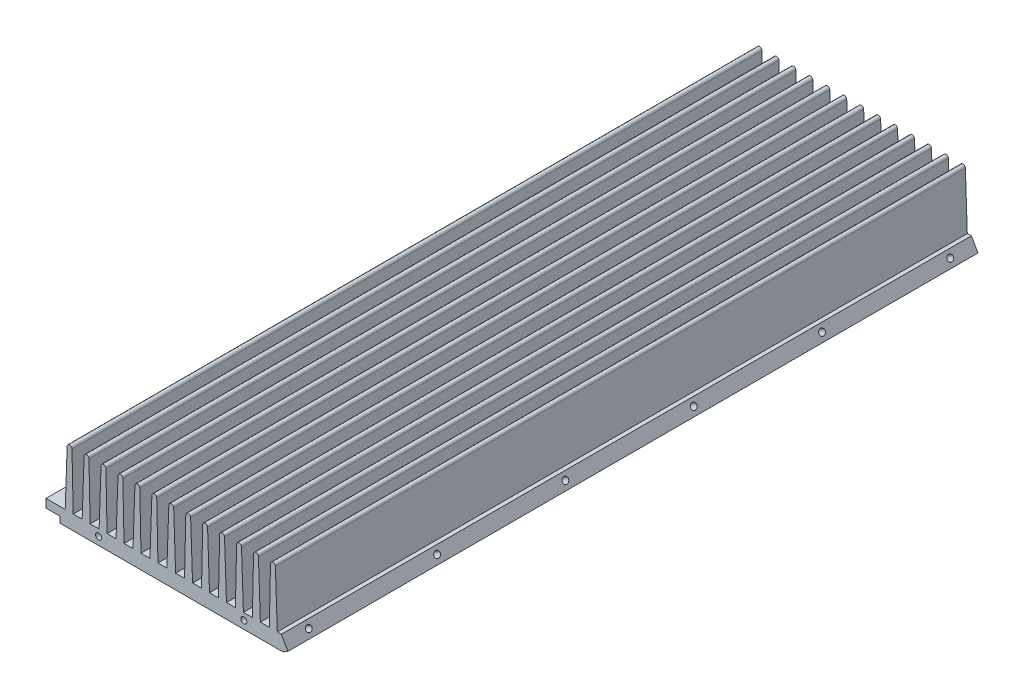
SolidWorks part; units mm, degrees
ref_plane "Plano frontal" through (0, 0, 0) normal (0, 0, 1) x (1, 0, 0)
ref_plane "Plano superior" through (0, 0, 0) normal (0, 1, 0) x (1, 0, 0)
ref_plane "Plano direito" through (0, 0, 0) normal (1, 0, 0) x (0, 0, -1)
sketch "Esboço1" plane through (0, 0, 0) normal (0, 0, 1) x (1, 0, 0)
  line L3 (0, 0) -> (-113, 0)
  line L102 (-76, 6) -> (-72.3, 6)
  line L103 (-83, 6) -> (-79.3, 6)
  line L104 (-86.3, 6) -> (-90, 6)
  line L115 (-56.5, 0) -> (-56.5, 30) construction
  line L116 (-113, 30) -> (15.3408, 30) construction
  line L146 (-86.3, 6) -> (-85.5, 29)
  line L147 (-83.5, 29) -> (-83, 6)
  line L148 (-85.5, 29) -> (-83.5, 29) construction
  line L149 (-90, 6) -> (-90.5, 29)
  line L150 (-92.5, 29) -> (-93.3, 6)
  line L151 (-48.5, 29) -> (-50.5, 29) construction
  line L152 (-93.3, 6) -> (-97, 6)
  line L153 (-97, 6) -> (-97.5, 29)
  line L154 (-99.5, 29) -> (-100.3, 6)
  line L155 (-79.3, 6) -> (-78.5, 29)
  line L156 (-76.5, 29) -> (-76, 6)
  line L161 (-78.5, 29) -> (-76.5, 29) construction
  line L162 (-72.3, 6) -> (-71.5, 29)
  line L163 (-100.3, 6) -> (-104, 6)
  line L164 (-71.5, 29) -> (-69.5, 29) construction
  line L165 (-69.5, 29) -> (-69, 6)
  line L167 (-104, 6) -> (-104.5, 29)
  line L169 (-8.5, 29) -> (-6.5, 29) construction
  line L170 (-90.5, 29) -> (-92.5, 29) construction
  line L171 (-97.5, 29) -> (-99.5, 29) construction
  line L172 (-104.5, 29) -> (-106.5, 29) construction
  line L173 (-15.5, 29) -> (-13.5, 29) construction
  line L174 (-22.5, 29) -> (-20.5, 29) construction
  line L175 (-107.3, 6) -> (-106.5, 29)
  line L176 (-113, 0) -> (-113, 30)
  line L177 (-113, 30) -> (-111, 30)
  line L178 (-111, 30) -> (-111, 6)
  line L179 (-111, 6) -> (-107.3, 6)
  line L181 (-57.5, 29) -> (-55.5, 29) construction
  line L183 (-69, 6) -> (-65.3, 6)
  line L184 (-65.3, 6) -> (-64.5, 29)
  line L185 (-64.5, 29) -> (-62.5, 29) construction
  line L186 (-62.5, 29) -> (-62, 6)
  line L187 (-62, 6) -> (-58.3, 6)
  line L188 (-58.3, 6) -> (-57.5, 29)
  line L189 (-41.5, 29) -> (-43.5, 29) construction
  line L190 (-34.5, 29) -> (-36.5, 29) construction
  line L191 (-27.5, 29) -> (-29.5, 29) construction
  line L192 (-54.7, 6) -> (-55.5, 29)
  line L193 (-51, 6) -> (-54.7, 6)
  line L194 (-50.5, 29) -> (-51, 6)
  line L195 (-47.7, 6) -> (-48.5, 29)
  line L196 (-44, 6) -> (-47.7, 6)
  line L197 (-2, 6) -> (-5.7, 6)
  line L198 (-2, 30) -> (-2, 6)
  line L199 (0, 30) -> (-2, 30)
  line L200 (0, 0) -> (0, 30)
  line L201 (-5.7, 6) -> (-6.5, 29)
  line L202 (-9, 6) -> (-8.5, 29)
  line L203 (-43.5, 29) -> (-44, 6)
  line L204 (-12.7, 6) -> (-9, 6)
  line L205 (-40.7, 6) -> (-41.5, 29)
  line L206 (-36.5, 29) -> (-37, 6)
  line L207 (-33.7, 6) -> (-34.5, 29)
  line L208 (-13.5, 29) -> (-12.7, 6)
  line L209 (-16, 6) -> (-15.5, 29)
  line L210 (-19.7, 6) -> (-16, 6)
  line L211 (-20.5, 29) -> (-19.7, 6)
  line L212 (-23, 6) -> (-22.5, 29)
  line L213 (-29.5, 29) -> (-30, 6)
  line L214 (-26.7, 6) -> (-27.5, 29)
  line L215 (-26.7, 6) -> (-23, 6)
  line L216 (-30, 6) -> (-33.7, 6)
  line L217 (-37, 6) -> (-40.7, 6)
  arc A4 (-85.5, 29) -> (-83.5, 29) centre (-84.5, 29) cw
  arc A6 (-78.5, 29) -> (-76.5, 29) centre (-77.5, 29) cw
  arc A8 (-71.5, 29) -> (-69.5, 29) centre (-70.5, 29) cw
  arc A20 (-90.5, 29) -> (-92.5, 29) centre (-91.5, 29) ccw
  arc A21 (-99.5, 29) -> (-97.5, 29) centre (-98.5, 29) cw
  arc A22 (-106.5, 29) -> (-104.5, 29) centre (-105.5, 29) cw
  arc A29 (-57.5, 29) -> (-55.5, 29) centre (-56.5, 29) cw
  arc A30 (-64.5, 29) -> (-62.5, 29) centre (-63.5, 29) cw
  arc A31 (-48.5, 29) -> (-50.5, 29) centre (-49.5, 29) ccw
  arc A32 (-6.5, 29) -> (-8.5, 29) centre (-7.5, 29) ccw
  arc A33 (-13.5, 29) -> (-15.5, 29) centre (-14.5, 29) ccw
  arc A34 (-22.5, 29) -> (-20.5, 29) centre (-21.5, 29) cw
  arc A35 (-41.5, 29) -> (-43.5, 29) centre (-42.5, 29) ccw
  arc A36 (-34.5, 29) -> (-36.5, 29) centre (-35.5, 29) ccw
  arc A37 (-27.5, 29) -> (-29.5, 29) centre (-28.5, 29) ccw
  point P43 (-56.5, 30)
  dimension "D2" = 1
  dimension "D1" = 7
  dimension "D3" = 3.7
  dimension "D4" = 2
  dimension "D5" = 6
  dimension "D6" = 113
  dimension "D8" = 30
extrude "Ressalto-extrusão1" add sketch "Esboço1" along normal blind 285
sketch "Esboço2" plane through (0, 0, 285) normal (0, 0, 1) x (1, 0, 0)
  line L5 (-102.5538, 0) -> (-10.4462, 0) construction
  line L6 (-102.8905, 6) -> (-108.2341, 6)
  line L16 (-108.2341, 6) -> (-108.2341, 2.5)
  line L22 (-108.2341, 2.5) -> (-102.5538, 2.5)
  line L23 (-8.2811, 1.25) -> (-10.4462, 0)
  line L25 (-102.5538, 2.5) -> (-102.5538, 0)
  line L26 (-100.3, 6) -> (-104, 6) construction
  line L27 (-113, 0) -> (0, 0) construction
  line L28 (-10.4462, 0) -> (0, 0)
  line L29 (0, 0) -> (0, 38.5588)
  line L30 (0, 38.5588) -> (-11.4168, 38.5588)
  line L31 (-11.4168, 38.5588) -> (-11.4168, 6.6812)
  line L34 (-11.4168, 6.6812) -> (-8.2811, 1.25)
  line L48 (-102.8905, 6) -> (-102.8905, 31.5406)
  line L49 (-102.8905, 31.5406) -> (-125.5568, 31.5406)
  line L50 (-125.5568, 31.5406) -> (-125.5568, -3.4367)
  line L51 (-125.5568, -3.4367) -> (-107.9645, -3.4367)
  line L52 (-107.9645, -3.4367) -> (-102.5538, 0)
  point P13 (-56.5, 0)
  point P14 (-56.5, 0)
  dimension "D1" = 92.1077
  dimension "D2" = 3.5
  dimension "D4" = 150
  dimension "D6" = 2.5
extrude "Corte-extrusão1" cut sketch "Esboço2" against normal through all both and the other way through all
sketch "Esboço11" [suppressed] plane through (0, 0, 285) normal (0, 0, 1) x (1, 0, 0)
  line L0 (-8.9831, 2.5341) -> (-8.2505, 1.2653)
  line L1 (-8.2505, 1.2653) -> (-10.4462, 0)
  line L2 (-10.4462, 0) -> (-11.3698, 0)
  line L4 (-11.3698, 0) -> (-10.7953, 3.3074)
  line L5 (-10.7953, 3.3074) -> (-8.9831, 2.5341)
  dimension "D1" = 8.2505
  dimension "D2" = 1.2653
  dimension "D3" = 2.1956
  dimension "D4" = 1.2653
  dimension "D5" = 1.2688
  dimension "D6" = 0.7326
extrude "Ressalto-extrusão5" [suppressed] add sketch "Esboço11" against normal blind 285
sketch "Esboço9" [suppressed] plane through (0, 0, 285) normal (0, 0, 1) x (1, 0, 0)
  line L2 (-6.9821, 6) -> (-8.9831, 2.5341) construction
  line L4 (-8.9821, 2.5359) -> (-10.9821, 6)
  line L5 (-16, 6) -> (-19.7, 6) construction
  line L6 (-10.9821, 6) -> (-6.9821, 6)
  line L7 (-6.9821, 6) -> (-8.9821, 2.5359)
  dimension "D1" = 4
sketch "Esboço3" [suppressed] plane through (0, 0, 285) normal (0, 0, 1) x (1, 0, 0)
  line L1 (-97, 6) -> (-122.3763, 6)
  line L2 (-97, 6) -> (-97, 40.0777)
  line L3 (-97, 40.0777) -> (-122.3763, 40.0777)
  line L4 (-122.3763, 6) -> (-122.3763, 40.0777)
  line L5 (-16, 6) -> (6.6432, 6)
  line L6 (-16, 6) -> (-16, 36.7002)
  line L7 (-16, 36.7002) -> (6.6432, 36.7002)
  line L8 (6.6432, 6) -> (6.6432, 36.7002)
extrude "Corte-extrusão2" [suppressed] cut sketch "Esboço3" against normal through all both and the other way through all
sketch "Esboço4" plane through (0, 0, 285) normal (0, 0, 1) x (1, 0, 0)
  line L0 (-56.5, 30) -> (-56.5, 0) construction
  line L1 (-102.5538, 0) -> (-10.4462, 0) construction
  line L2 (-86.5, 3.2348) -> (-56.5, 3.2348) construction
  line L3 (-56.5, 3.2348) -> (-26.5, 3.2348) construction
  circle A0 centre (-26.5, 3.2348) radius 1.25
  circle A1 centre (-86.5, 3.2348) radius 1.25
  arc A2 (-55.5, 29) -> (-57.5, 29) centre (-56.5, 29) ccw construction
  dimension "D3" = 2.5
  dimension "D1" = 30
  dimension "D2" = 3.2348
extrude "Corte-extrusão3" cut sketch "Esboço4" against normal blind 10
sketch "Esboço5" [suppressed] plane through (0, 6, 0) normal (0, 1, 0) x (1, 0, 0)
  line L0 (-99.0329, -274.5) -> (-99.0329, -208.5) construction
  line L1 (-99.0329, -208.5) -> (-99.0329, -142.5) construction
  line L2 (-99.0329, -142.5) -> (-99.0329, -76.5) construction
  line L3 (-99.0329, -76.5) -> (-99.0329, -10.5) construction
  line L4 (-106.0179, 0) -> (-106.0179, -285) construction
  line L5 (-100.3, -285) -> (-113, -285) construction
  circle A0 centre (-99.0329, -274.5) radius 1.25
  circle A1 centre (-99.0329, -208.5) radius 1.25
  circle A2 centre (-99.0329, -142.5) radius 1.25
  circle A3 centre (-99.0329, -76.5) radius 1.25
  circle A4 centre (-99.0329, -10.5) radius 1.25
  circle A5 centre (-12.4646, -20.5) radius 1.25
  circle A6 centre (-12.4646, -101.8333) radius 1.25
  circle A7 centre (-12.4646, -183.1667) radius 1.25
  circle A8 centre (-12.4646, -264.5) radius 1.25
  dimension "D1" = 2.5
  dimension "D3" = 10.5
  dimension "D2" = 6.985
  dimension "D4" = 66
extrude "Corte-extrusão4" [suppressed] cut sketch "Esboço5" against normal blind 5
sketch "Esboço6" [suppressed] plane through (0, 0, 0) normal (0, 0, -1) x (-1, 0, 0)
  line L0 (6.9821, 6) -> (10.4462, 0) construction
  line L1 (8.7141, 3) -> (104.2859, 3) construction
  line L2 (102.5538, 0) -> (106.0179, 6) construction
  line L3 (103.7085, 2) -> (9.2915, 2)
  line L4 (9.2915, 2) -> (8.1368, 4)
  line L5 (8.1368, 4) -> (104.8632, 4)
  line L6 (104.8632, 4) -> (103.7085, 2)
  line L7 (102.5538, 0) -> (106.0179, 6) construction
  line L8 (6.9821, 6) -> (10.4462, 0) construction
  line L9 (6.9821, 6) -> (19.7, 6) construction
  point P11 (104.2859, 3)
  dimension "D1" = 1
  dimension "D2" = 1
extrude "Ressalto-extrusão2" [suppressed] add sketch "Esboço6" along normal blind 1
sketch "Esboço7" plane through (0, 0, 0) normal (0, -1, 0) x (-1, 0, 0)
  line L0 (49.75, -279) -> (49.75, -275.2034) construction
  line L1 (49.75, -275.2034) -> (63.25, -275.2034) construction
  line L2 (102.5538, -285) -> (10.4462, -285) construction
  line L3 (63.25, -275.2034) -> (63.25, -279) construction
  line L6 (56.5, -275.2034) -> (56.5, -279) construction
  line L7 (10.4462, -279) -> (102.5538, -279) construction
  line L8 (10.4462, 0) -> (10.4462, -285) construction
  line L9 (102.5538, 0) -> (102.5538, -285) construction
  circle A0 centre (95, -28.5) radius 1.65
  circle A1 centre (71.949, -28.592) radius 1.25
  circle A2 centre (72.33, -10.685) radius 1.25
  circle A3 centre (30.928, -51.5) radius 1.25
  circle A4 centre (24, -15) radius 1.65
  circle A5 centre (34.738, -79.011) radius 1.25
  circle A6 centre (18.355, -144.416) radius 1.65
  circle A7 centre (20, -249) radius 1.65
  circle A8 centre (35.246, -237) radius 1.25
  circle A9 centre (93, -249) radius 1.65
  circle A10 centre (78.807, -182.77) radius 1.25
  circle A11 centre (82.363, -100.093) radius 1.25
  circle A12 centre (29.404, -176.293) radius 1.25
  circle A13 centre (39, -220) radius 1.25
  circle A14 centre (39, -200) radius 1.25
  circle A15 centre (39, -180) radius 1.25
  circle A16 centre (39, -160) radius 1.25
  circle A17 centre (74, -130) radius 1.25
  circle A18 centre (74, -110) radius 1.25
  circle A19 centre (74, -90) radius 1.25
  circle A20 centre (74, -70) radius 1.25
  circle A21 centre (92.7378, -168.3478) radius 1.25
  circle A22 centre (94.207, -195.6022) radius 1.25
  circle A23 centre (89.5041, -51.5) radius 1.25
  circle A28 centre (49.75, -279) radius 1.25
  circle A29 centre (63.25, -279) radius 1.25
  dimension "D1" = 3.3
  dimension "D2" = 2.5
  dimension "D3" = 2.5
  dimension "D4" = 2.5
  dimension "D5" = 2.5
  dimension "D6" = 2.5
  dimension "D7" = 6
  dimension "D8" = 13.5
extrude "Corte-extrusão5" cut sketch "Esboço7" against normal blind 4
sketch "Esboço12" [suppressed] plane through (0, 0, 285) normal (0, 0, 1) x (1, 0, 0)
  line L0 (-86.5, 3.2348) -> (-26.5, 3.2348)
  line L1 (-56.5, 3.2348) -> (-56.5, 0)
  line L2 (-102.5538, 0) -> (-10.4462, 0) construction
sketch "Esboço13" plane through (0, 2.5, 0) normal (0, -1, 0) x (1, 0, 0)
  line L0 (-105.394, 275) -> (-105.394, 222) construction
  line L3 (-105.394, 222) -> (-105.394, 169) construction
  line L4 (-105.394, 169) -> (-105.394, 116) construction
  line L5 (-105.394, 116) -> (-105.394, 63) construction
  line L6 (-105.394, 63) -> (-105.394, 10) construction
  line L7 (-105.394, 10) -> (-105.394, 0) construction
  line L8 (-102.5538, 0) -> (-108.2341, 0) construction
  line L9 (-105.394, 275) -> (-105.394, 285) construction
  line L10 (-102.5538, 285) -> (-108.2341, 285) construction
  circle A0 centre (-105.394, 275) radius 1.75
  circle A1 centre (-105.394, 222) radius 1.75
  circle A2 centre (-105.394, 169) radius 1.75
  circle A3 centre (-105.394, 63) radius 1.75
  circle A4 centre (-105.394, 10) radius 1.75
  circle A5 centre (-105.394, 116) radius 1.75
  dimension "D1" = 3.5
  dimension "D3" = 10
extrude "Corte-extrusão8" cut sketch "Esboço13" against normal through all both and the other way through all
sketch "Esboço14" plane through (-5.6696, -3.2733, 0) normal (0.866, 0.5, 0) x (0, 0, -1)
  line L0 (-285, 10.7079) -> (-285, 5.2231) construction
  line L2 (0, 5.2231) -> (-285, 5.2231) construction
  circle A0 centre (-275, 8.0632) radius 1.25
  circle A1 centre (-222, 8.0632) radius 1.25
  circle A2 centre (-169, 8.0632) radius 1.25
  circle A3 centre (-116, 8.0632) radius 1.25
  circle A4 centre (-63, 8.0632) radius 1.25
  circle A5 centre (-10, 8.0632) radius 1.25
  dimension "D1" = 2.5
  dimension "D2" = 10
  dimension "D4" = 53
  dimension "D5" = 2.8401
  dimension "D3" = 6
extrude "Corte-extrusão9" cut sketch "Esboço14" against normal blind 5
sketch "Esboço15" [suppressed] plane through (-56.5028, 0, 0) normal (-1, 0, 0) x (0, 0, 1)
  line L0 (281, 3) -> (281, 0)
  line L1 (285, 3) -> (281, 3)
  line L2 (285, 0) -> (285, 2.5) construction
  line L4 (0, 0) -> (285, 0) construction
  line L5 (281, 0) -> (285, 0)
  line L6 (285, 0) -> (285, 3)
  dimension "D1" = 3
  dimension "D3" = 4
extrude "Corte-extrusão10" [suppressed] cut sketch "Esboço15" against normal mid plane 62
